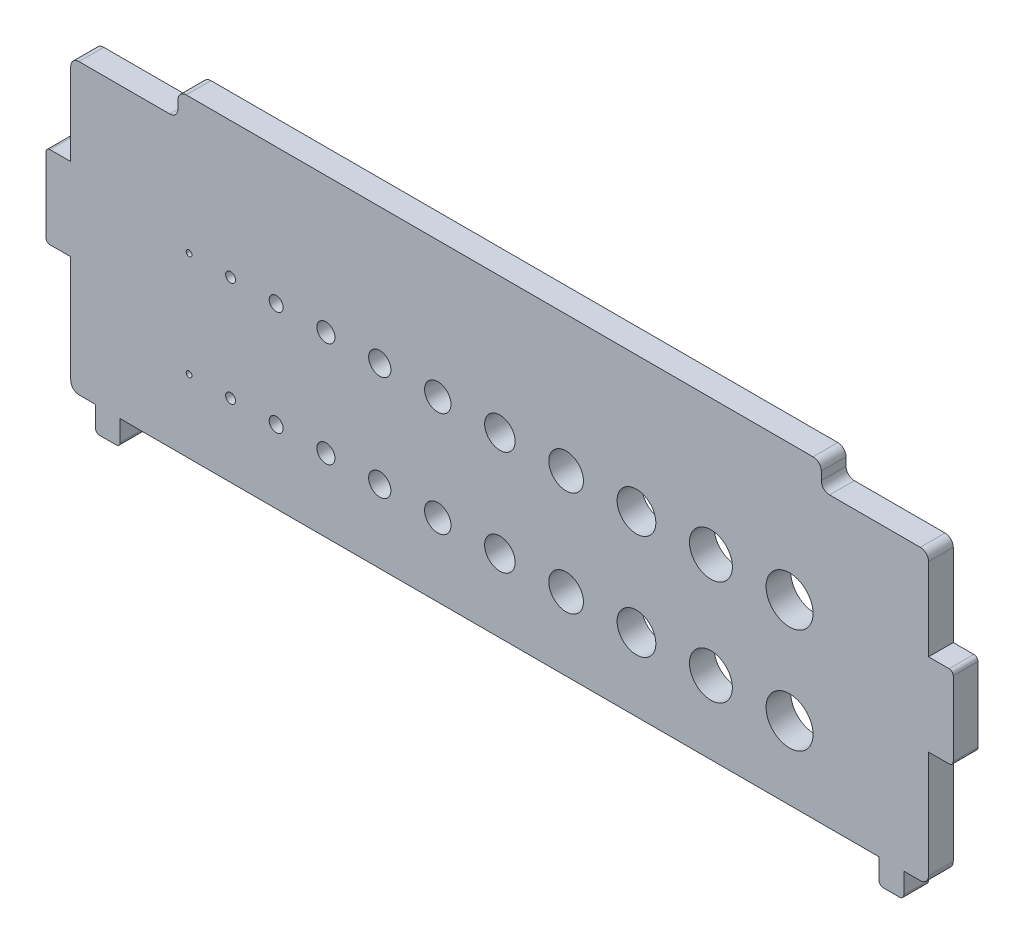
SolidWorks part; units mm, degrees
ref_plane "Спереди" through (0, 0, 0) normal (0, 0, 1) x (1, 0, 0)
ref_plane "Сверху" through (0, 0, 0) normal (0, 1, 0) x (1, 0, 0)
ref_plane "Справа" through (0, 0, 0) normal (1, 0, 0) x (0, 0, -1)
sketch "Эскиз1" plane through (0, 0, 0) normal (0, 0, 1) x (1, 0, 0)
  line L0 (0, 0) -> (0, 24.1439) construction
  line L1 (-52, 19) -> (52, 19)
  line L2 (-52, 19) -> (-52, -19)
  line L3 (-52, -19) -> (-49, -19)
  line L4 (52, 19) -> (52, -19)
  line L5 (-52, 19) -> (52, -19) construction
  line L6 (-52, -19) -> (52, 19) construction
  line L7 (52, 5) -> (55, 5)
  line L8 (52, 5) -> (52, -5)
  line L9 (52, -5) -> (55, -5)
  line L10 (55, 5) -> (55, -5)
  line L11 (52, 5) -> (55, -5) construction
  line L12 (52, -5) -> (55, 5) construction
  line L13 (-52, -5) -> (-55, 5) construction
  line L14 (-52, 5) -> (-55, -5) construction
  line L15 (-55, 5) -> (-55, -5)
  line L16 (-52, -5) -> (-55, -5)
  line L17 (-52, 5) -> (-52, -5)
  line L18 (-52, 5) -> (-55, 5)
  line L19 (-52, 16) -> (-39, 16)
  line L20 (-39, 16) -> (-39, 19)
  line L21 (39, 16) -> (39, 19)
  line L22 (52, 16) -> (39, 16)
  line L23 (32.3, 2.55) -> (28.22, 2.55) construction
  line L24 (23.02, 2.55) -> (18.94, 2.55) construction
  line L25 (18.94, 2.55) -> (14.24, 2.55) construction
  line L26 (14.24, 2.55) -> (10.16, 2.55) construction
  line L27 (10.16, 2.55) -> (5.96, 2.55) construction
  line L28 (5.96, 2.55) -> (1.88, 2.55) construction
  line L29 (1.88, 2.55) -> (-1.82, 2.55) construction
  line L30 (-1.82, 2.55) -> (-5.9, 2.55) construction
  line L31 (-5.9, 2.55) -> (-9.1, 2.55) construction
  line L32 (-9.1, 2.55) -> (-13.18, 2.55) construction
  line L33 (-13.18, 2.55) -> (-15.88, 2.55) construction
  line L34 (-15.88, 2.55) -> (-19.96, 2.55) construction
  line L35 (-19.96, 2.55) -> (-22.16, 2.55) construction
  line L36 (-22.16, 2.55) -> (-26.24, 2.55) construction
  line L37 (-26.24, 2.55) -> (-27.94, 2.55) construction
  line L38 (-27.94, 2.55) -> (-32.02, 2.55) construction
  line L39 (-32.02, 2.55) -> (-33.22, 2.55) construction
  line L40 (-33.22, 2.55) -> (-37.3, 2.55) construction
  line L41 (32.3, -10.15) -> (28.22, -10.15) construction
  line L42 (23.02, -10.15) -> (18.94, -10.15) construction
  line L43 (18.94, -10.15) -> (14.24, -10.15) construction
  line L44 (14.24, -10.15) -> (10.16, -10.15) construction
  line L45 (10.16, -10.15) -> (5.96, -10.15) construction
  line L46 (5.96, -10.15) -> (1.88, -10.15) construction
  line L47 (1.88, -10.15) -> (-1.82, -10.15) construction
  line L48 (-1.82, -10.15) -> (-5.9, -10.15) construction
  line L49 (-5.9, -10.15) -> (-9.1, -10.15) construction
  line L50 (-9.1, -10.15) -> (-13.18, -10.15) construction
  line L51 (-13.18, -10.15) -> (-15.88, -10.15) construction
  line L52 (-15.88, -10.15) -> (-19.96, -10.15) construction
  line L53 (-19.96, -10.15) -> (-22.16, -10.15) construction
  line L54 (-22.16, -10.15) -> (-26.24, -10.15) construction
  line L55 (-26.24, -10.15) -> (-27.94, -10.15) construction
  line L56 (-27.94, -10.15) -> (-32.02, -10.15) construction
  line L57 (-32.02, -10.15) -> (-33.22, -10.15) construction
  line L58 (-33.22, -10.15) -> (-37.3, -10.15) construction
  line L59 (0, -19) -> (46, -19)
  line L64 (49, -19) -> (52, -19)
  line L65 (-46, -19) -> (0, -19)
  line L66 (-49, -22) -> (-46, -19) construction
  line L68 (49, -19) -> (49, -22)
  line L69 (49, -22) -> (46, -22)
  line L70 (46, -19) -> (46, -22)
  line L71 (49, -19) -> (46, -22) construction
  line L72 (49, -22) -> (46, -19) construction
  line L73 (-49, -19) -> (-46, -22) construction
  line L74 (-46, -19) -> (-46, -22)
  line L75 (-49, -22) -> (-46, -22)
  line L76 (-49, -19) -> (-49, -22)
  circle A12 centre (-7.5, 2.55) radius 1.6
  circle A13 centre (-14.53, 2.55) radius 1.35
  circle A14 centre (-21.06, 2.55) radius 1.1
  circle A15 centre (-27.09, 2.55) radius 0.85
  circle A16 centre (-32.62, 2.55) radius 0.6
  circle A17 centre (-37.65, 2.55) radius 0.35
  circle A18 centre (35.15, 2.55) radius 2.85
  circle A19 centre (25.62, 2.55) radius 2.6
  circle A20 centre (16.59, 2.55) radius 2.35
  circle A21 centre (8.06, 2.55) radius 2.1
  circle A22 centre (0.03, 2.55) radius 1.85
  circle A23 centre (-7.5, -10.15) radius 1.6
  circle A24 centre (-14.53, -10.15) radius 1.35
  circle A25 centre (-21.06, -10.15) radius 1.1
  circle A26 centre (-27.09, -10.15) radius 0.85
  circle A27 centre (-32.62, -10.15) radius 0.6
  circle A28 centre (-37.65, -10.15) radius 0.35
  circle A29 centre (35.15, -10.15) radius 2.85
  circle A30 centre (25.62, -10.15) radius 2.6
  circle A31 centre (16.59, -10.15) radius 2.35
  circle A32 centre (8.06, -10.15) radius 2.1
  circle A33 centre (0.03, -10.15) radius 1.85
  point P0 (0, 0)
  point P6 (53.5, 0)
  point P17 (-53.5, 0)
  point P67 (0, -12.7)
  point P114 (47.5, -20.5)
  point P123 (-47.5, -20.5)
  dimension "D5" = 14
  dimension "D7" = 5.2
  dimension "D6" = 5.7
  dimension "D8" = 4.7
  dimension "D11" = 4.2
  dimension "D15" = 3.7
  dimension "D16" = 6
  dimension "D17" = 7
  dimension "D20" = 3
  dimension "D21" = 3
  dimension "D9" = 14
  dimension "D10" = 0.7
  dimension "D14" = 2
  dimension "D22" = 3.2
  dimension "D23" = 2.7
  dimension "D24" = 2.2
  dimension "D25" = 1.7
  dimension "D26" = 1.2
  dimension "D1" = 3
  dimension "D2" = 10
  dimension "D3" = 38
  dimension "D4" = 110
  dimension "D12" = 13
  dimension "D13" = 3
extrude "Бобышка-Вытянуть1" add sketch "Эскиз1" along normal blind 3
fillet "Скругление1" radius 0.5 8 edges at (-55, 5, 1.5) (-55, -5, 1.5) (55, -5, 1.5) (55, 5, 1.5) (49, -22, 1.5) (46, -22, 1.5) (-46, -22, 1.5) (-49, -22, 1.5)
fillet "Скругление2" radius 1 8 edges at (-52, -19, 1.5) (-52, 16, 1.5) (-39, 16, 1.5) (-39, 19, 1.5) (39, 19, 1.5) (39, 16, 1.5) (52, 16, 1.5) (52, -19, 1.5)
equation "\"a\"= 0 , 2"
